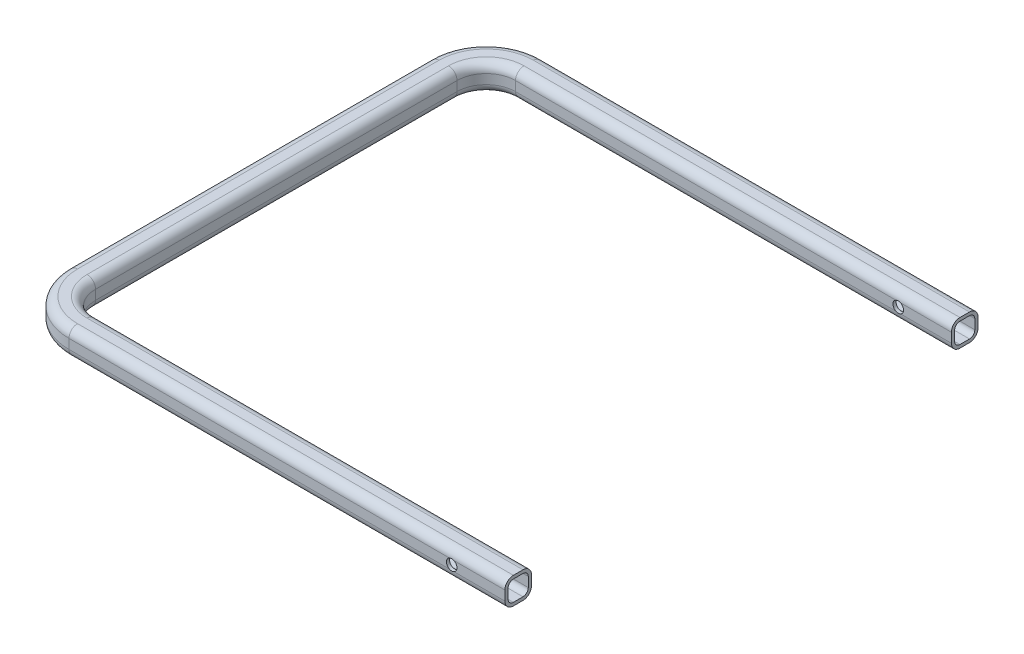
SolidWorks part; units mm, degrees
ref_plane "Front Plane" through (0, 0, 0) normal (0, 0, 1) x (1, 0, 0)
ref_plane "Top Plane" through (0, 0, 0) normal (0, 1, 0) x (1, 0, 0)
ref_plane "Right Plane" through (0, 0, 0) normal (1, 0, 0) x (0, 0, -1)
sketch "Sketch1" plane through (0, 0, 0) normal (0, 1, 0) x (1, 0, 0)
  line L0 (0, 0) -> (-410, 0)
  line L1 (-450, 40) -> (-450, 380)
  line L2 (-410, 420) -> (0, 420)
  line L3 (-50, 0) -> (-50, 420) construction
  arc A0 (-410, 0) -> (-450, 40) centre (-410, 40) cw
  arc A1 (-410, 420) -> (-450, 380) centre (-410, 380) ccw
  point P7 (-450, 0)
  point P10 (-450, 420)
  dimension "D3" = 40
  dimension "D1" = 450
  dimension "D2" = 420
  dimension "D4" = 50
sketch "Sketch2" plane through (0, 0, 0) normal (1, 0, 0) x (0, 0, -1)
  line L1 (-4.5, -9.5) -> (4.5, -9.5)
  line L2 (-9.5, -4.5) -> (-9.5, 4.5)
  line L3 (-4.5, 9.5) -> (4.5, 9.5)
  line L4 (9.5, -4.5) -> (9.5, 4.5)
  line L5 (-9.5, -9.5) -> (9.5, 9.5) construction
  line L6 (-9.5, 9.5) -> (9.5, -9.5) construction
  arc A0 (-4.5, 9.5) -> (-9.5, 4.5) centre (-4.5, 4.5) ccw
  arc A1 (-9.5, -4.5) -> (-4.5, -9.5) centre (-4.5, -4.5) ccw
  arc A2 (4.5, -9.5) -> (9.5, -4.5) centre (4.5, -4.5) ccw
  arc A3 (9.5, 4.5) -> (4.5, 9.5) centre (4.5, 4.5) ccw
  point P0 (0, 0)
  dimension "D3" = 5
  dimension "D1" = 19
  dimension "D2" = 19
sweep "Sweep-Thin1" add profiles "Sketch2" path "Sketch1" parameters "D1"=3
sketch "Sketch3" plane through (0, 0, 0) normal (0, 0, 1) x (1, 0, 0)
  line L0 (0, 0) -> (-410, 0) construction
  circle A0 centre (-50, 0) radius 5
  dimension "D1" = 50
extrude "Cut-Extrude1" cut sketch "Sketch3" against normal through all and the other way through all
sketch "Sketch4" plane through (0, 0, -12.5) normal (0, 0, -1) x (-1, 0, 0)
  line L0 (0, 0) -> (45, 0) construction
  line L1 (0, -4.5) -> (0, 4.5) construction
  arc A0 (47.8206, 4.5) -> (47.8206, -4.5) centre (50, 0) ccw construction
ref_plane "Plane1" through (-450, 0, 0) normal (1, 0, 0) x (0, 0, -1)
sketch "Sketch5" plane through (-450, 0, 0) normal (1, 0, 0) x (0, 0, -1)
  line L0 (380, 0) -> (38.7593, 0) construction
  line L1 (209.3797, 0) -> (281.8797, 0) construction
  line L3 (209.3797, 0) -> (136.8797, 0) construction
  line L4 (281.8797, 0) -> (281.8797, -50) construction
  line L5 (136.8797, 0) -> (136.8797, -50) construction
  dimension "D1" = 72.5
  dimension "D2" = 72.5
